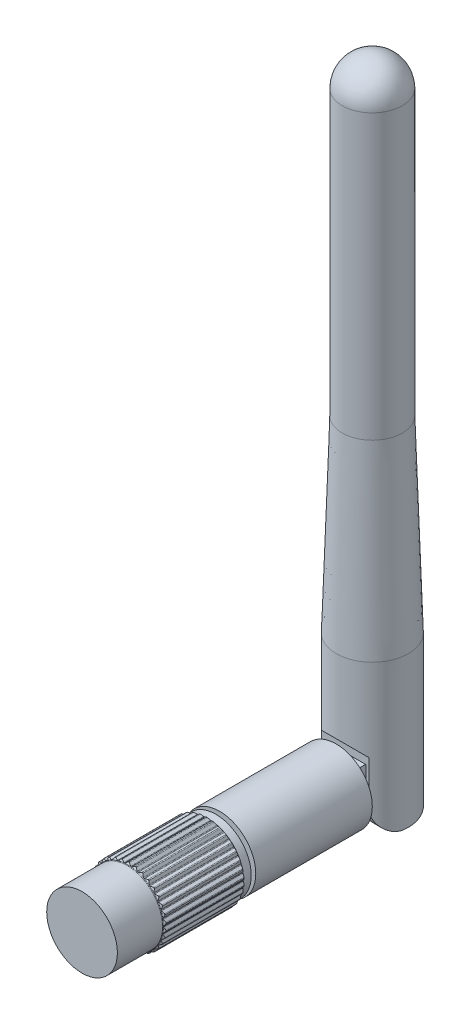
SolidWorks part; units mm, degrees
ref_plane "Front Plane" through (0, 0, 0) normal (0, 0, 1) x (1, 0, 0)
ref_plane "Top Plane" through (0, 0, 0) normal (0, 1, 0) x (1, 0, 0)
ref_plane "Right Plane" through (0, 0, 0) normal (1, 0, 0) x (0, 0, -1)
sketch "Sketch1" plane through (0, 0, 0) normal (1, 0, 0) x (0, 0, -1)
  line L0 (0, 0) -> (4.8, 0)
  line L1 (4.8, 0) -> (4.8, 20)
  line L2 (4.8, 20) -> (4, 45)
  line L3 (4, 45) -> (4, 82.7)
  line L4 (0, 0) -> (0, 86.7)
  line L5 (0, 86.7) -> (7.0365, 86.7) construction
  arc A0 (4, 82.7) -> (0, 86.7) centre (0, 82.7) ccw
  dimension "D1" = 86.7
  dimension "D2" = 4.8
  dimension "D3" = 4
  dimension "D4" = 20
  dimension "D5" = 25
revolve "Revolve1" add sketch "Sketch1" angle 360 about L4
sketch "Sketch2" plane through (0, 0, 0) normal (0, -1, 0) x (1, 0, 0)
  line L1 (-2.75, 4.8) -> (2.75, 4.8)
  line L2 (-2.75, 4.8) -> (-2.75, -3)
  line L3 (-2.75, -3) -> (2.75, -3)
  line L4 (2.75, 4.8) -> (2.75, -3)
  circle A1 centre (0, 0) radius 4.8 construction
  dimension "D1" = 5.5
  dimension "D2" = 3
  dimension "D3" = 2.75
extrude "Cut-Extrude1" cut sketch "Sketch2" against normal blind 8
sketch "Sketch4" plane through (0, 0, 0) normal (1, 0, 0) x (0, 0, -1)
  line L0 (-4.8, 10.2) -> (-3.6, 9)
  line L1 (-4.8, 20) -> (-4.8, 8) construction
  line L2 (-3.6, 9) -> (-3.6, 3)
  line L3 (-3.9341, 0) -> (4.8, 0) construction
  line L4 (-0.6, 0) -> (-4.8, 0)
  line L5 (-4.8, 0) -> (-4.8, 10.2)
  arc A0 (-3.6, 3) -> (-0.6, 0) centre (-0.6, 3) ccw
  dimension "D4" = 3
  dimension "D1" = 45
  dimension "D2" = 1.2
  dimension "D3" = 9
extrude "Cut-Extrude2" cut sketch "Sketch4" against normal up to next and the other way up to next
sketch "Sketch3" plane through (-2.75, 0, 0) normal (1, 0, 0) x (0, 0, -1)
  line L0 (-4.8, 7.7) -> (-4.8, 1.9)
  line L1 (-4.8, 1.9) -> (0, 1.9)
  line L2 (0, 7.7) -> (-4.8, 7.7)
  line L3 (-0.6, 0) -> (4.8, 0) construction
  arc A0 (0, 1.9) -> (0, 7.7) centre (0, 4.8) ccw
  dimension "D1" = 5.8
  dimension "D2" = 4.8
  dimension "D3" = 4.8
extrude "Boss-Extrude1" add sketch "Sketch3" along normal blind 4.8 from offset 0.35 separate body
sketch "Sketch5" plane through (0, 0, 4.8) normal (0, 0, 1) x (1, 0, 0)
  line L0 (2.4, 1.9) -> (-2.4, 1.9) construction
  circle A0 centre (0, 4.8) radius 4.8
  dimension "D1" = 9.6
  dimension "D2" = 2.9
extrude "Boss-Extrude2" add sketch "Sketch5" along normal blind 15.5
sketch "Sketch6" plane through (0, 0, 20.3) normal (0, 0, 1) x (1, 0, 0)
  circle A0 centre (0, 4.8) radius 3.5
  dimension "D1" = 7
extrude "Boss-Extrude3" add sketch "Sketch6" along normal blind 0.5
sketch "Sketch7" plane through (0, 0, 20.8) normal (0, 0, 1) x (1, 0, 0)
  circle A0 centre (0, 4.8) radius 4.7
  dimension "D1" = 9.4
extrude "Boss-Extrude4" add sketch "Sketch7" along normal blind 17.8
sketch "Sketch8" plane through (0, 0, 38.6) normal (0, 0, 1) x (1, 0, 0)
  line L0 (0, 4.8) -> (-0.4337, 0.12) construction
  line L1 (0, 4.8) -> (0.4337, 0.12) construction
  line L2 (-0.4337, 0.12) -> (-0.4383, 0.0703)
  line L3 (-0.366, 0.046) -> (-0.0723, -0.1758)
  line L4 (0.0723, -0.1758) -> (0.366, 0.046)
  line L5 (0.4383, 0.0703) -> (0.4337, 0.12)
  line L6 (0.4337, 0.12) -> (-0.4337, 0.12)
  line L7 (-0.4383, 0.0703) -> (0.4383, 0.0703) construction
  circle A0 centre (0, 4.8) radius 5 construction
  circle A1 centre (0, 4.8) radius 4.7 construction
  arc A2 (-0.4383, 0.0703) -> (-0.366, 0.046) centre (-0.4383, -0.0497) cw
  arc A3 (-0.0723, -0.1758) -> (0.0723, -0.1758) centre (0, -0.08) ccw
  arc A4 (0.366, 0.046) -> (0.4383, 0.0703) centre (0.4383, -0.0497) cw
  dimension "D1" = 10
  dimension "D2" = 0.12
  dimension "D3" = 0.05
  dimension "D4" = 10.588
extrude "Boss-Extrude5" add sketch "Sketch8" against normal blind 10.8 from offset 6 offset against normal yes
pattern_circular "CirPattern1" count 34 over 360 about axis through (0, 4.8, 0) along (0, 0, 1) of "Boss-Extrude5"
sketch "Sketch9" plane through (0, 0, 0) normal (1, 0, 0) x (0, 0, -1)
  line L0 (-32.6, 9.4058) -> (-32.6, 9.6777) construction
  line L1 (-32.5134, 9.55) -> (-32.3979, 9.75)
  line L2 (-21.8, 9.8) -> (-32.6, 9.8) construction
  line L3 (-32.6, 9.5) -> (-32.6, 9.8)
  line L4 (-32.6, 9.8) -> (-32.6, 9.7758) construction
  line L5 (-32.6, 9.8) -> (-32.3113, 9.8)
  line L6 (-21.8, 9.4058) -> (-21.8, 9.6777) construction
  line L7 (-21.8866, 9.55) -> (-22.0021, 9.75)
  line L8 (-22.0887, 9.8) -> (-21.8, 9.8)
  line L9 (-21.8, 9.7758) -> (-21.8, 9.8) construction
  line L10 (-21.8, 9.8) -> (-21.8, 9.5)
  line L11 (-21.8, 9.5) -> (-32.6, 9.5) construction
  line L12 (-20.8, 9.5) -> (-21.8, 9.5) construction
  line L13 (-20.8, 4.8) -> (-38.6, 4.8) construction
  line L14 (-20.8, 0.1) -> (-20.8, 9.5) construction
  line L15 (-38.6, 9.5) -> (-38.6, 0.1) construction
  arc A0 (-32.6, 9.5) -> (-32.5134, 9.55) centre (-32.6, 9.6) ccw
  arc A1 (-32.3979, 9.75) -> (-32.3113, 9.8) centre (-32.3113, 9.7) cw
  arc A2 (-21.8, 9.5) -> (-21.8866, 9.55) centre (-21.8, 9.6) cw
  arc A3 (-22.0021, 9.75) -> (-22.0887, 9.8) centre (-22.0887, 9.7) ccw
  dimension "D4" = 0.1
  dimension "D1" = 0.3
  dimension "D2" = 30
  dimension "D3" = 30
revolve "Cut-Revolve1" cut sketch "Sketch9" angle 360 about L13
